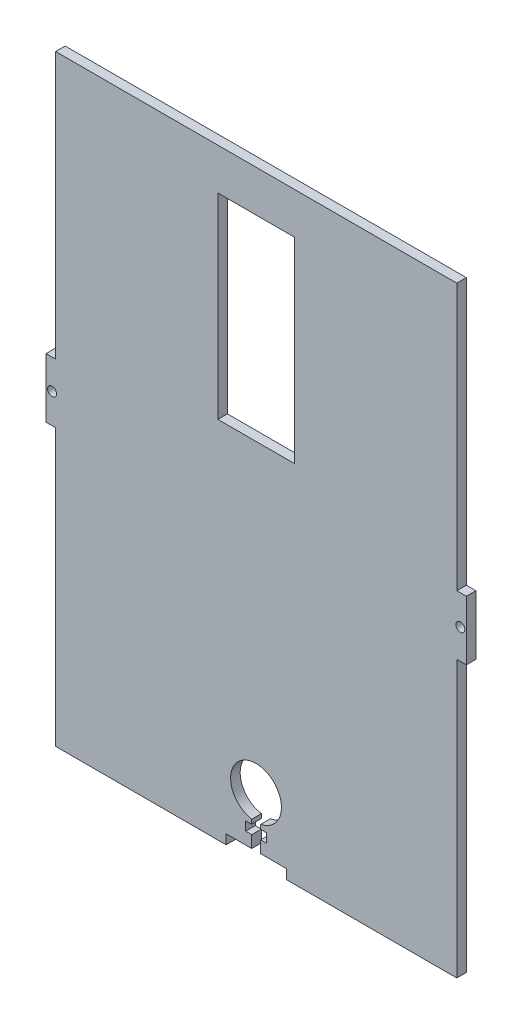
SolidWorks part; units mm, degrees
ref_plane "Front Plane" through (0, 0, 0) normal (0, 0, 1) x (1, 0, 0)
ref_plane "Top Plane" through (0, 0, 0) normal (0, 1, 0) x (1, 0, 0)
ref_plane "Right Plane" through (0, 0, 0) normal (1, 0, 0) x (0, 0, -1)
sketch "Sketch1" plane through (0, 0, 0) normal (0, 0, 1) x (1, 0, 0)
  line L1 (-69.85, 101.6) -> (69.85, 101.6)
  line L2 (-69.85, 101.6) -> (-69.85, -101.6)
  line L3 (-69.85, -101.6) -> (69.85, -101.6)
  line L4 (69.85, 101.6) -> (69.85, -101.6)
  line L5 (-69.85, 101.6) -> (69.85, -101.6) construction
  line L6 (-69.85, -101.6) -> (69.85, 101.6) construction
  point P0 (0, 0)
  dimension "D1" = 203.2
  dimension "D2" = 139.7
extrude "Boss-Extrude1" add sketch "Sketch1" along normal blind 3.18
sketch "Sketch2" plane through (0, 0, 3.18) normal (0, 0, 1) x (1, 0, 0)
  line L0 (0, 0) -> (69.85, 0) construction
  line L1 (-10, 101.6) -> (10, 101.6)
  line L2 (-10, 101.6) -> (-10, 98.42)
  line L3 (-10, 98.42) -> (-1.5, 98.42)
  line L4 (10, 101.6) -> (10, 98.42)
  line L5 (69.85, -101.6) -> (69.85, 101.6) construction
  line L6 (0, 0) -> (0, 101.6) construction
  line L7 (-1.5, 88.42) -> (1.5, 88.42)
  line L8 (-1.5, 88.42) -> (-1.5, 91.42)
  line L10 (1.5, 88.42) -> (1.5, 91.42)
  line L12 (69.85, 101.6) -> (-69.85, 101.6) construction
  line L13 (3.5, 94.42) -> (1.5, 94.42)
  line L14 (3.5, 94.42) -> (3.5, 91.42)
  line L15 (3.5, 91.42) -> (1.5, 91.42)
  line L16 (-3.5, 94.42) -> (-3.5, 91.42)
  line L17 (-10, -101.6) -> (-10, -98.42)
  line L18 (-10, -98.42) -> (-1.5, -98.42)
  line L19 (-1.5, -94.42) -> (-1.5, -98.42)
  line L20 (-1.5, -94.42) -> (-3.5, -94.42)
  line L21 (-3.5, -94.42) -> (-3.5, -91.42)
  line L22 (1.5, 98.42) -> (10, 98.42)
  line L23 (-1.5, 94.42) -> (-3.5, 94.42)
  line L24 (-1.5, -91.42) -> (-3.5, -91.42)
  line L25 (-1.5, -88.42) -> (-1.5, -91.42)
  line L26 (-1.5, -88.42) -> (1.5, -88.42)
  line L27 (-1.5, 91.42) -> (-3.5, 91.42)
  line L28 (1.5, -88.42) -> (1.5, -91.42)
  line L29 (-1.5, 94.42) -> (-1.5, 98.42)
  line L30 (1.5, 94.42) -> (1.5, 98.42)
  line L31 (3.5, -91.42) -> (1.5, -91.42)
  line L32 (3.5, -94.42) -> (3.5, -91.42)
  line L33 (3.5, -94.42) -> (1.5, -94.42)
  line L34 (1.5, -94.42) -> (1.5, -98.42)
  line L35 (1.5, -98.42) -> (10, -98.42)
  line L36 (10, -101.6) -> (10, -98.42)
  line L37 (-10, -101.6) -> (10, -101.6)
  line L38 (-69.85, 101.6) -> (-69.85, -101.6) construction
  line L39 (-69.85, 101.6) -> (-66.67, 101.6)
  line L40 (-69.85, 101.6) -> (-69.85, 9.875)
  line L41 (-69.85, 9.875) -> (-66.67, 9.875)
  line L42 (-66.67, 101.6) -> (-66.67, 9.875)
  line L43 (-69.85, -101.6) -> (-66.67, -101.6)
  line L44 (-69.85, -101.6) -> (-69.85, -9.875)
  line L45 (-69.85, -9.875) -> (-66.67, -9.875)
  line L46 (-66.67, -101.6) -> (-66.67, -9.875)
  line L47 (69.85, -9.875) -> (66.67, -9.875)
  line L48 (66.67, -101.6) -> (66.67, -9.875)
  line L49 (69.85, -101.6) -> (66.67, -101.6)
  line L50 (69.85, -101.6) -> (69.85, -9.875)
  line L51 (69.85, 9.875) -> (66.67, 9.875)
  line L52 (66.67, 101.6) -> (66.67, 9.875)
  line L53 (69.85, 101.6) -> (66.67, 101.6)
  line L54 (69.85, 101.6) -> (69.85, 9.875)
  circle A0 centre (-67.85, 0) radius 1.5
  circle A1 centre (67.85, 0) radius 1.5
  point P0 (0, 50.5662)
  point P5 (0, 32.0079)
  point P10 (15.4931, 34.4893)
  dimension "D11" = 3
  dimension "D12" = 2
  dimension "D1" = 20
  dimension "D2" = 19.75
  dimension "D3" = 4
  dimension "D4" = 3
  dimension "D5" = 3.18
  dimension "D6" = 7
  dimension "D7" = 3
  dimension "D8" = 3
  dimension "D9" = 3.18
  dimension "D10" = 3.18
extrude "Cut-Extrude1" cut sketch "Sketch2" against normal through all
sketch "Sketch3" plane through (0, 0, 0) normal (0, 0, -1) x (-1, 0, 0)
  circle A0 centre (0.0688, -81.6486) radius 8.442
extrude "Cut-Extrude2" cut sketch "Sketch3" against normal blind 10 contours A0
sketch "Sketch5" plane through (0, 0, 0) normal (0, 0, -1) x (-1, 0, 0)
  line L1 (12.7653, 84.6626) -> (-12.7653, 84.6626)
  line L2 (12.7653, 84.6626) -> (12.7653, 19.4862)
  line L3 (12.7653, 19.4862) -> (-12.7653, 19.4862)
  line L4 (-12.7653, 84.6626) -> (-12.7653, 19.4862)
  line L5 (12.7653, 84.6626) -> (-12.7653, 19.4862) construction
  line L6 (12.7653, 19.4862) -> (-12.7653, 84.6626) construction
  point P0 (0, 52.0744)
extrude "Cut-Extrude3" cut sketch "Sketch5" against normal blind 10
sketch "Sketch6" plane through (0, 0, 0) normal (0, 0, -1) x (-1, 0, 0)
  line L1 (-10, 101.6) -> (10.5427, 101.6)
  line L2 (-10, 101.6) -> (-10, 87.1954)
  line L3 (-10, 87.1954) -> (10.5427, 87.1954)
  line L4 (10.5427, 101.6) -> (10.5427, 87.1954)
extrude "Boss-Extrude2" add sketch "Sketch6" against normal blind 3.18
sketch "Sketch7" plane through (0, 0, 0) normal (0, 0, -1) x (-1, 0, 0)
  line L1 (-66.67, 101.6) -> (-10.036, 101.6)
  line L2 (-66.67, 101.6) -> (-66.67, 98.42)
  line L3 (-66.67, 98.42) -> (-10.036, 98.42)
  line L4 (-10.036, 101.6) -> (-10.036, 98.42)
  line L5 (66.67, 101.6) -> (9.714, 101.6)
  line L6 (66.67, 101.6) -> (66.67, 98.42)
  line L7 (66.67, 98.42) -> (9.714, 98.42)
  line L8 (9.714, 101.6) -> (9.714, 98.42)
  dimension "D1" = 3.18
  dimension "D2" = 3.18
  dimension "D3" = 19.75
extrude "Cut-Extrude4" cut sketch "Sketch7" against normal blind 3.18
sketch "Sketch8" plane through (-9.714, 0, 0) normal (-1, 0, 0) x (0, 0, 1)
  line L1 (0, 98.42) -> (3.18, 98.42)
  line L2 (0, 98.42) -> (0, 101.6)
  line L3 (0, 101.6) -> (3.18, 101.6)
  line L4 (3.18, 98.42) -> (3.18, 101.6)
extrude "Cut-Extrude5" cut sketch "Sketch8" against normal through all
